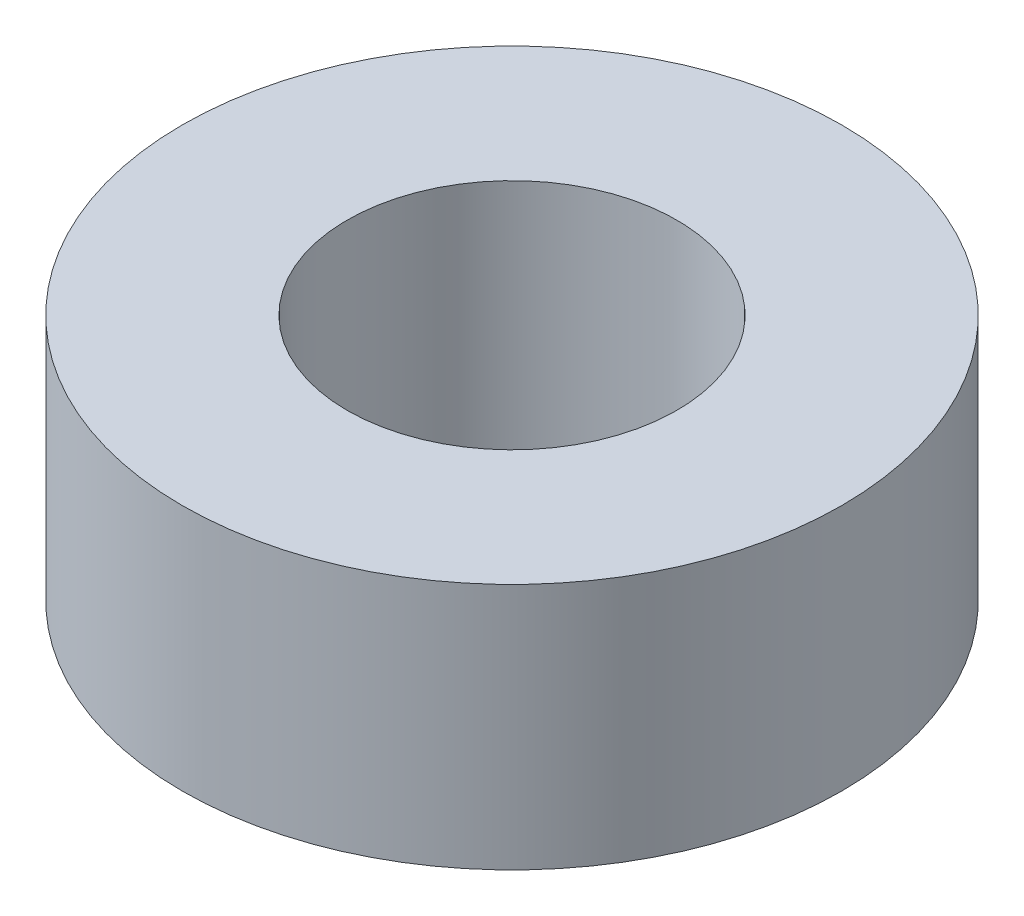
SolidWorks part; units mm, degrees
ref_plane "Front Plane" through (0, 0, 0) normal (0, 0, 1) x (1, 0, 0)
ref_plane "Top Plane" through (0, 0, 0) normal (0, 1, 0) x (1, 0, 0)
ref_plane "Right Plane" through (0, 0, 0) normal (1, 0, 0) x (0, 0, -1)
sketch "Sketch1" plane through (0, 0, 0) normal (0, 1, 0) x (1, 0, 0)
  circle A0 centre (0, 0) radius 6.35
  circle A1 centre (0, 0) radius 3.175
  dimension "D1" = 12.7
  dimension "D2" = 6.35
extrude "Boss-Extrude1" add sketch "Sketch1" along normal blind 4.7625
